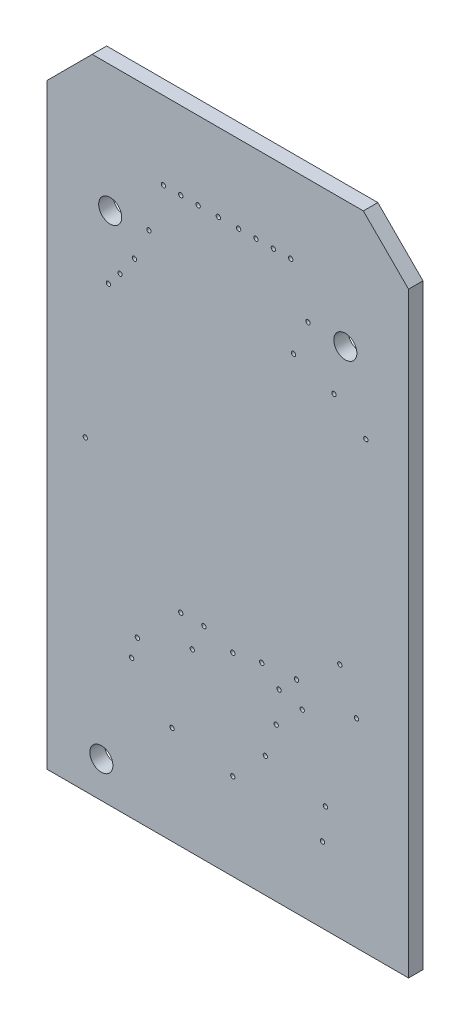
SolidWorks part; units mm, degrees
ref_plane "Front Plane" through (0, 0, 0) normal (0, 0, 1) x (1, 0, 0)
ref_plane "Top Plane" through (0, 0, 0) normal (0, 1, 0) x (1, 0, 0)
ref_plane "Right Plane" through (0, 0, 0) normal (1, 0, 0) x (0, 0, -1)
ref_plane "Dielectric_Layer Layer 1" through (0, 0, 0.9144) normal (0, 0, 1) x (1, 0, 0)
sketch "Sketch1" plane through (0, 0, 0) normal (0, 0, 1) x (1, 0, 0)
  line L0 (0, 0) -> (0, 20.955)
  line L1 (0, 20.955) -> (1.5875, 22.5425)
  line L2 (1.5875, 22.5425) -> (11.1125, 22.5425)
  line L3 (11.1125, 22.5425) -> (12.7, 20.955)
  line L4 (12.7, 20.955) -> (12.7, 0)
  line L5 (12.7, 0) -> (0, 0)
extrude "Board_Outline" add sketch "Sketch1" along normal blind 0.508 separate body
sketch "Sketch2" plane through (0, 0, 0) normal (0, 0, 1) x (1, 0, 0)
  circle A0 centre (10.287, 8.3312) radius 0.0762
  circle A1 centre (7.6708, 4.2418) radius 0.0762
  circle A2 centre (6.731, 19.812) radius 0.0762
  circle A3 centre (11.2014, 15.6464) radius 0.0762
  circle A4 centre (5.3086, 19.812) radius 0.0762
  circle A5 centre (2.5654, 16.3576) radius 0.0762
  circle A6 centre (4.699, 19.812) radius 0.0762
  circle A7 centre (3.0734, 17.0688) radius 0.0762
  circle A8 centre (4.0894, 19.812) radius 0.0762
  circle A9 centre (3.5814, 18.1864) radius 0.0762
  circle A10 centre (8.5598, 19.812) radius 0.0762
  circle A11 centre (8.6614, 16.9672) radius 0.0762
  circle A12 centre (7.9502, 19.812) radius 0.0762
  circle A13 centre (9.1694, 18.1864) radius 0.0762
  circle A14 centre (7.3406, 19.812) radius 0.0762
  circle A15 centre (10.0838, 16.4592) radius 0.0762
  circle A16 centre (6.0198, 19.812) radius 0.0762
  circle A17 centre (2.159, 15.8496) radius 0.0762
  circle A18 centre (4.699, 7.112) radius 0.0762
  circle A19 centre (3.175, 5.588) radius 0.0762
  circle A20 centre (4.3942, 3.4544) radius 0.0762
  circle A21 centre (2.9718, 4.8768) radius 0.0762
  circle A22 centre (5.5118, 7.112) radius 0.0762
  circle A23 centre (6.5278, 6.8072) radius 0.0762
  circle A24 centre (6.5278, 3.048) radius 0.0762
  circle A25 centre (9.6774, 2.6416) radius 0.0762
  circle A26 centre (7.5438, 7.0104) radius 0.0762
  circle A27 centre (5.1054, 6.1976) radius 0.0762
  circle A28 centre (9.779, 3.7592) radius 0.0762
  circle A29 centre (8.9662, 6.2992) radius 0.0762
  circle A30 centre (8.763, 7.112) radius 0.0762
  circle A31 centre (8.1534, 6.5024) radius 0.0762
  circle A32 centre (8.0518, 5.3848) radius 0.0762
  circle A33 centre (1.3462, 10.7696) radius 0.0762
  circle A34 centre (10.8712, 6.985) radius 0.0762
extrude "NPTH" cut sketch "Sketch2" along normal through all
sketch "Sketch3" plane through (0, 0, 0) normal (0, 0, 1) x (1, 0, 0)
  circle A0 centre (2.22, 18.1) radius 0.405
  circle A1 centre (10.48, 18.1) radius 0.405
  circle A2 centre (1.91, 1.27) radius 0.405
extrude "PTH" cut sketch "Sketch3" along normal through all
